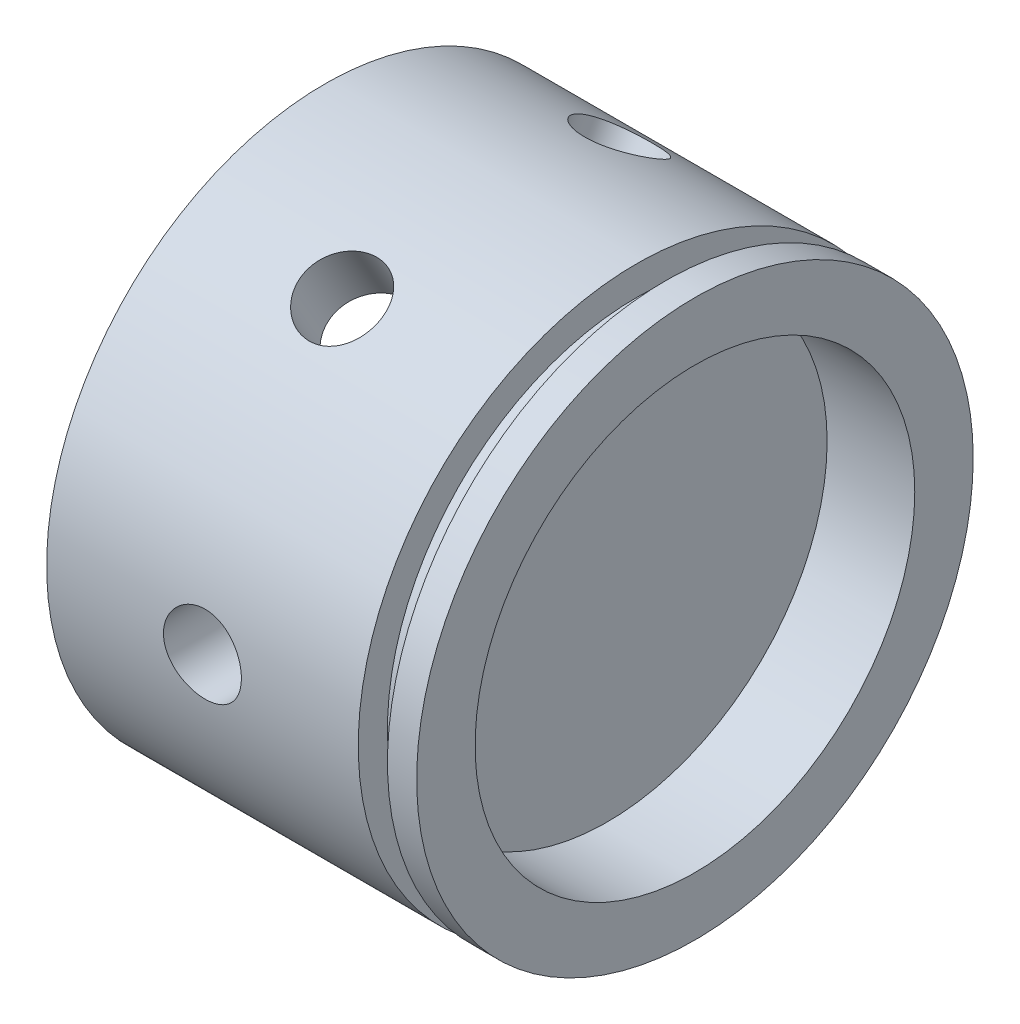
SolidWorks part; units mm, degrees
material "AISI 1020"
ref_plane "Plano frontal" through (0, 0, 0) normal (0, 0, 1) x (1, 0, 0)
ref_plane "Plano superior" through (0, 0, 0) normal (0, 1, 0) x (1, 0, 0)
ref_plane "Plano direito" through (0, 0, 0) normal (1, 0, 0) x (0, 0, -1)
sketch "Esboço1" plane through (0, 0, 0) normal (0, 0, 1) x (1, 0, 0)
  line L0 (0, 0) -> (-50000, 0) construction
  line L1 (0, -1000) -> (0, 49000) construction
  line L2 (35, 28.575) -> (38, 28.575)
  line L7 (0, 28.575) -> (32, 28.575)
  line L8 (0, 28.575) -> (0, 22.575)
  line L9 (0, 22.575) -> (24, 22.575)
  line L10 (38, 28.575) -> (38, 22.575)
  line L12 (24, 22.575) -> (24, 0)
  line L13 (24, 0) -> (29, 0)
  line L14 (29, 22.575) -> (29, 0)
  line L16 (32, 28.575) -> (32, 25.575)
  line L17 (32, 25.575) -> (35, 25.575)
  line L18 (35, 28.575) -> (35, 25.575)
  line L19 (29, 22.575) -> (38, 22.575)
  point P17 (20, 28.575)
  point P18 (12, 28.575)
  dimension "D1" = 28.575
  dimension "D2" = 8
  dimension "D3" = 12
  dimension "D4" = 4
  dimension "D5" = 3
  dimension "D6" = 3
  dimension "D7" = 3
  dimension "D8" = 3
  dimension "D9" = 5
  dimension "D10" = 3
revolve "Revolução1" add sketch "Esboço1" angle 360 about L0
sketch "Esboço2" plane through (0, 0, 0) normal (0, 0, 1) x (1, 0, 0)
  line L0 (-1000, 0) -> (49000, 0) construction
  circle A0 centre (16, 0) radius 4
  point P5 (12, 0)
  dimension "D1" = 8
  dimension "D2" = 12
extrude "Corte-extrusão1" cut sketch "Esboço2" against normal blind 60
pattern_circular "PadrãoCircular1" count 6 over 360 about axis through (0, 0, 0) along (1, 0, 0) of "Corte-extrusão1"
equation "\"D1@Esboço1\"=25.4*(2.5-2*(1/8))/2"
equation "\"D3@Esboço1\"=1.5*\"D2@Esboço1\""
equation "\"D2@Esboço2\"=1.5*\"D1@Esboço2\""
